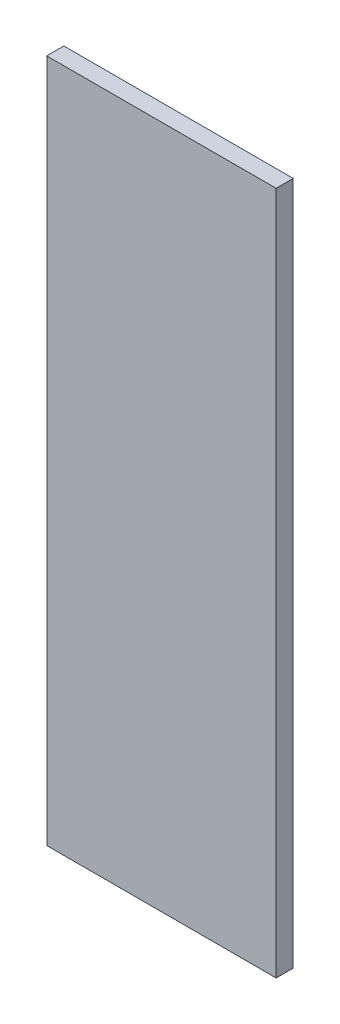
SolidWorks part; units mm, degrees
ref_plane "Front Plane" through (0, 0, 0) normal (0, 0, 1) x (1, 0, 0)
ref_plane "Top Plane" through (0, 0, 0) normal (0, 1, 0) x (1, 0, 0)
ref_plane "Right Plane" through (0, 0, 0) normal (1, 0, 0) x (0, 0, -1)
sketch "Sketch1" plane through (0, 0, 0) normal (0, 0, 1) x (1, 0, 0)
  line L1 (-21.2985, -63.5) -> (21.2985, -63.5)
  line L2 (-21.2985, -63.5) -> (-21.2985, 63.5)
  line L3 (-21.2985, 63.5) -> (21.2985, 63.5)
  line L4 (21.2985, -63.5) -> (21.2985, 63.5)
  line L5 (-21.2985, -63.5) -> (21.2985, 63.5) construction
  line L6 (-21.2985, 63.5) -> (21.2985, -63.5) construction
  point P0 (0, 0)
  dimension "D1" = 127
  dimension "D2" = 42.5971
extrude "Boss-Extrude1" add sketch "Sketch1" along normal blind 3.175
